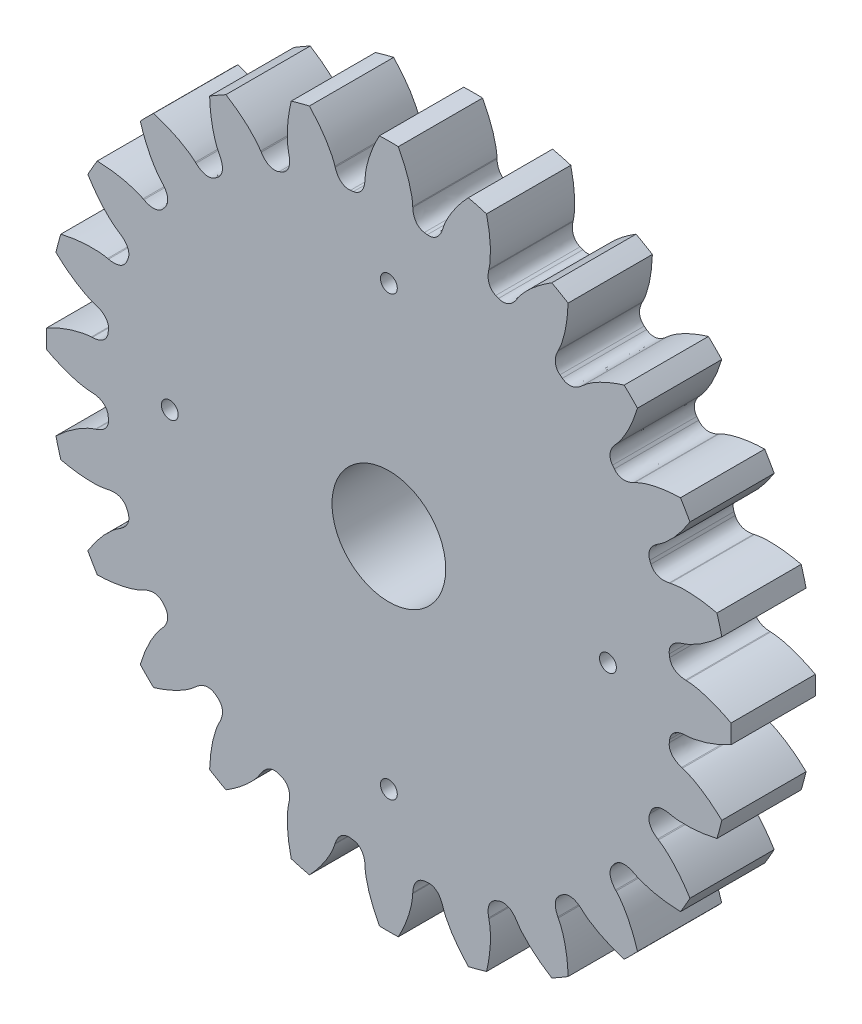
SolidWorks part; units mm, degrees
material "PET"
ref_plane "Front Plane" through (0, 0, 0) normal (0, 0, 1) x (1, 0, 0)
ref_plane "Top Plane" through (0, 0, 0) normal (0, 1, 0) x (1, 0, 0)
ref_plane "Right Plane" through (0, 0, 0) normal (1, 0, 0) x (0, 0, -1)
sketch "Sketch1" plane through (0, 0, 0) normal (0, 0, 1) x (1, 0, 0)
  line L2 (3.0163, 8.479) -> (3.0105, 8.452)
  line L3 (3.8478, 8.1052) -> (3.8627, 8.1284)
  line L4 (5.8144, 6.8332) -> (5.8349, 6.8516)
  line L5 (5.108, 7.4094) -> (5.0955, 7.3849)
  line L6 (7.3849, 5.0955) -> (7.4094, 5.108)
  line L7 (6.8516, 5.8349) -> (6.8332, 5.8144)
  line L8 (8.452, 3.0105) -> (8.479, 3.0163)
  line L9 (8.1284, 3.8627) -> (8.1052, 3.8478)
  line L10 (8.9432, 0.7204) -> (8.9707, 0.719)
  line L11 (8.8511, 1.6273) -> (8.8249, 1.6189)
  line L12 (8.8249, -1.6189) -> (8.8511, -1.6273)
  line L13 (8.9707, -0.719) -> (8.9432, -0.7204)
  line L14 (8.1052, -3.8478) -> (8.1284, -3.8627)
  line L15 (8.479, -3.0163) -> (8.452, -3.0105)
  line L16 (6.8332, -5.8144) -> (6.8516, -5.8349)
  line L17 (7.4094, -5.108) -> (7.3849, -5.0955)
  line L18 (5.0955, -7.3849) -> (5.108, -7.4094)
  line L19 (5.8349, -6.8516) -> (5.8144, -6.8332)
  line L20 (3.0105, -8.452) -> (3.0163, -8.479)
  line L21 (3.8627, -8.1284) -> (3.8478, -8.1052)
  line L22 (0.7204, -8.9432) -> (0.719, -8.9707)
  line L23 (1.6273, -8.8511) -> (1.6189, -8.8249)
  line L24 (-1.6189, -8.8249) -> (-1.6273, -8.8511)
  line L25 (-0.719, -8.9707) -> (-0.7204, -8.9432)
  line L26 (-3.8478, -8.1052) -> (-3.8627, -8.1284)
  line L27 (-3.0163, -8.479) -> (-3.0105, -8.452)
  line L28 (-5.8144, -6.8332) -> (-5.8349, -6.8516)
  line L29 (-5.108, -7.4094) -> (-5.0955, -7.3849)
  line L30 (-7.3849, -5.0955) -> (-7.4094, -5.108)
  line L31 (-6.8516, -5.8349) -> (-6.8332, -5.8144)
  line L32 (-8.452, -3.0105) -> (-8.479, -3.0163)
  line L33 (-8.1284, -3.8627) -> (-8.1052, -3.8478)
  line L34 (-8.9432, -0.7204) -> (-8.9707, -0.719)
  line L35 (-8.8511, -1.6273) -> (-8.8249, -1.6189)
  line L36 (-8.8249, 1.6189) -> (-8.8511, 1.6273)
  line L37 (-8.9707, 0.719) -> (-8.9432, 0.7204)
  line L38 (-8.1052, 3.8478) -> (-8.1284, 3.8627)
  line L39 (-8.479, 3.0163) -> (-8.452, 3.0105)
  line L40 (-6.8332, 5.8144) -> (-6.8516, 5.8349)
  line L41 (-7.4094, 5.108) -> (-7.3849, 5.0955)
  line L42 (-5.0955, 7.3849) -> (-5.108, 7.4094)
  line L43 (-5.8349, 6.8516) -> (-5.8144, 6.8332)
  line L44 (-3.0105, 8.452) -> (-3.0163, 8.479)
  line L45 (-3.8627, 8.1284) -> (-3.8478, 8.1052)
  line L46 (-0.7204, 8.9432) -> (-0.719, 8.9707)
  line L47 (-1.6273, 8.8511) -> (-1.6189, 8.8249)
  line L48 (1.6189, 8.8249) -> (1.6273, 8.8511)
  line L49 (0.719, 8.9707) -> (0.7204, 8.9432)
  arc A1 (5.4033, 8.7909) -> (4.9115, 9.0749) centre (0, 0) ccw
  arc A3 (3.3076, 7.8657) -> (3.223, 7.9007) centre (0, 0) ccw
  arc A4 (7.4945, 7.0929) -> (7.0929, 7.4945) centre (0, 0) ccw
  arc A5 (5.2307, 6.7416) -> (5.1581, 6.7973) centre (0, 0) ccw
  arc A6 (9.0749, 4.9115) -> (8.7909, 5.4033) centre (0, 0) ccw
  arc A7 (6.7973, 5.1581) -> (6.7416, 5.2307) centre (0, 0) ccw
  arc A8 (10.0369, 2.3954) -> (9.8899, 2.944) centre (0, 0) ccw
  arc A9 (7.9007, 3.223) -> (7.8657, 3.3076) centre (0, 0) ccw
  arc A10 (10.3148, -0.284) -> (10.3148, 0.284) centre (0, 0) ccw
  arc A11 (8.4657, 1.0684) -> (8.4537, 1.1591) centre (0, 0) ccw
  arc A12 (9.8899, -2.944) -> (10.0369, -2.3954) centre (0, 0) ccw
  arc A13 (8.4537, -1.1591) -> (8.4657, -1.0684) centre (0, 0) ccw
  arc A14 (8.7909, -5.4033) -> (9.0749, -4.9115) centre (0, 0) ccw
  arc A15 (7.8657, -3.3076) -> (7.9007, -3.223) centre (0, 0) ccw
  arc A16 (7.0929, -7.4945) -> (7.4945, -7.0929) centre (0, 0) ccw
  arc A17 (6.7416, -5.2307) -> (6.7973, -5.1581) centre (0, 0) ccw
  arc A18 (4.9115, -9.0749) -> (5.4033, -8.7909) centre (0, 0) ccw
  arc A19 (5.1581, -6.7973) -> (5.2307, -6.7416) centre (0, 0) ccw
  arc A20 (2.3954, -10.0369) -> (2.944, -9.8899) centre (0, 0) ccw
  arc A21 (3.223, -7.9007) -> (3.3076, -7.8657) centre (0, 0) ccw
  arc A22 (-0.284, -10.3148) -> (0.284, -10.3148) centre (0, 0) ccw
  arc A23 (1.0684, -8.4657) -> (1.1591, -8.4537) centre (0, 0) ccw
  arc A24 (-2.944, -9.8899) -> (-2.3954, -10.0369) centre (0, 0) ccw
  arc A25 (-1.1591, -8.4537) -> (-1.0684, -8.4657) centre (0, 0) ccw
  arc A26 (-5.4033, -8.7909) -> (-4.9115, -9.0749) centre (0, 0) ccw
  arc A27 (-3.3076, -7.8657) -> (-3.223, -7.9007) centre (0, 0) ccw
  arc A28 (-7.4945, -7.0929) -> (-7.0929, -7.4945) centre (0, 0) ccw
  arc A29 (-5.2307, -6.7416) -> (-5.1581, -6.7973) centre (0, 0) ccw
  arc A30 (-9.0749, -4.9115) -> (-8.7909, -5.4033) centre (0, 0) ccw
  arc A31 (-6.7973, -5.1581) -> (-6.7416, -5.2307) centre (0, 0) ccw
  arc A32 (-10.0369, -2.3954) -> (-9.8899, -2.944) centre (0, 0) ccw
  arc A33 (-7.9007, -3.223) -> (-7.8657, -3.3076) centre (0, 0) ccw
  arc A34 (-10.3148, 0.284) -> (-10.3148, -0.284) centre (0, 0) ccw
  arc A35 (-8.4657, -1.0684) -> (-8.4537, -1.1591) centre (0, 0) ccw
  arc A36 (-9.8899, 2.944) -> (-10.0369, 2.3954) centre (0, 0) ccw
  arc A37 (-8.4537, 1.1591) -> (-8.4657, 1.0684) centre (0, 0) ccw
  arc A38 (-8.7909, 5.4033) -> (-9.0749, 4.9115) centre (0, 0) ccw
  arc A39 (-7.8657, 3.3076) -> (-7.9007, 3.223) centre (0, 0) ccw
  arc A40 (-7.0929, 7.4945) -> (-7.4945, 7.0929) centre (0, 0) ccw
  arc A41 (-6.7416, 5.2307) -> (-6.7973, 5.1581) centre (0, 0) ccw
  arc A42 (-4.9115, 9.0749) -> (-5.4033, 8.7909) centre (0, 0) ccw
  arc A43 (-5.1581, 6.7973) -> (-5.2307, 6.7416) centre (0, 0) ccw
  arc A44 (-2.3954, 10.0369) -> (-2.944, 9.8899) centre (0, 0) ccw
  arc A45 (-3.223, 7.9007) -> (-3.3076, 7.8657) centre (0, 0) ccw
  arc A46 (0.284, 10.3148) -> (-0.284, 10.3148) centre (0, 0) ccw
  arc A47 (-1.0684, 8.4657) -> (-1.1591, 8.4537) centre (0, 0) ccw
  arc A48 (2.944, 9.8899) -> (2.3954, 10.0369) centre (0, 0) ccw
  arc A49 (1.1591, 8.4537) -> (1.0684, 8.4657) centre (0, 0) ccw
  spline S1 degree 3 poles (3.8627, 8.1284) (3.8914, 8.1749) (3.9475, 8.2534) (4.0419, 8.3672) (4.1469, 8.48) (4.2788, 8.6067) (4.4396, 8.7446) (4.6307, 8.8906) (4.7925, 9.0003) (4.8899, 9.0615) (4.9115, 9.0749) knots 0.278297 0.278297 0.278297 0.278297 0.361423 0.4249 0.502987 0.595682 0.702987 0.8249 0.961423 1 1 1 1
  spline S3 degree 3 poles (3.3076, 7.8657) (3.3668, 7.8404) (3.4599, 7.8298) (3.5701, 7.8582) (3.6332, 7.8877) (3.6849, 7.9217) (3.7286, 7.9585) (3.7669, 7.9973) (3.8073, 8.0456) (3.8335, 8.0821) (3.8478, 8.1052) knots 0 0 0 0 0.297543 0.420013 0.525832 0.620051 0.707292 0.791048 0.873798 1 1 1 1
  spline S6 degree 3 poles (2.944, 9.8899) (2.9498, 9.8652) (2.9754, 9.7529) (3.0122, 9.561) (3.0441, 9.3226) (3.0603, 9.1114) (3.064, 8.9285) (3.0584, 8.7745) (3.0447, 8.6274) (3.0289, 8.5322) (3.0163, 8.479) knots 0 0 0 0 0.038577 0.1751 0.297013 0.404318 0.497013 0.5751 0.638577 0.721703 0.721703 0.721703 0.721703
  spline S7 degree 3 poles (3.0105, 8.452) (3.0042, 8.4256) (2.9969, 8.3813) (2.9914, 8.3186) (2.991, 8.264) (2.9959, 8.2071) (3.0084, 8.1465) (3.0321, 8.081) (3.09, 7.9831) (3.1633, 7.9247) (3.223, 7.9007) knots 0 0 0 0 0.126202 0.208952 0.292708 0.379949 0.474168 0.579987 0.702457 1 1 1 1
  spline S8 degree 3 poles (5.8349, 6.8516) (5.8746, 6.8892) (5.9492, 6.9505) (6.0698, 7.0359) (6.2004, 7.1178) (6.3606, 7.206) (6.5515, 7.2976) (6.774, 7.3892) (6.9586, 7.4532) (7.0686, 7.4872) (7.0929, 7.4945) knots 0.278297 0.278297 0.278297 0.278297 0.361423 0.4249 0.502987 0.595682 0.702987 0.8249 0.961423 1 1 1 1
  spline S9 degree 3 poles (5.2307, 6.7416) (5.2813, 6.7019) (5.3685, 6.6675) (5.4823, 6.6664) (5.5509, 6.6785) (5.6096, 6.6981) (5.6613, 6.7223) (5.7084, 6.7499) (5.76, 6.786) (5.7947, 6.8146) (5.8144, 6.8332) knots 0 0 0 0 0.297543 0.420013 0.525832 0.620051 0.707292 0.791048 0.873798 1 1 1 1
  spline S10 degree 3 poles (5.0955, 7.3849) (5.0826, 7.361) (5.064, 7.32) (5.0425, 7.2609) (5.0279, 7.2083) (5.018, 7.1521) (5.0143, 7.0903) (5.0203, 7.0209) (5.0509, 6.9113) (5.1066, 6.8359) (5.1581, 6.7973) knots 0 0 0 0 0.126202 0.208952 0.292708 0.379949 0.474168 0.579987 0.702457 1 1 1 1
  spline S11 degree 3 poles (5.4033, 8.7909) (5.4026, 8.7656) (5.3982, 8.6505) (5.3841, 8.4557) (5.3532, 8.217) (5.3142, 8.0089) (5.2704, 7.8313) (5.2252, 7.684) (5.1739, 7.5454) (5.134, 7.4575) (5.108, 7.4094) knots 0 0 0 0 0.038577 0.1751 0.297013 0.404318 0.497013 0.5751 0.638577 0.721703 0.721703 0.721703 0.721703
  spline S12 degree 3 poles (7.4094, 5.108) (7.4575, 5.134) (7.5454, 5.1739) (7.684, 5.2252) (7.8313, 5.2704) (8.0089, 5.3142) (8.217, 5.3532) (8.4557, 5.3841) (8.6505, 5.3982) (8.7656, 5.4026) (8.7909, 5.4033) knots 0.278297 0.278297 0.278297 0.278297 0.361423 0.4249 0.502987 0.595682 0.702987 0.8249 0.961423 1 1 1 1
  spline S13 degree 3 poles (6.7973, 5.1581) (6.8359, 5.1066) (6.9113, 5.0509) (7.0209, 5.0203) (7.0903, 5.0143) (7.1521, 5.018) (7.2083, 5.0279) (7.2609, 5.0425) (7.32, 5.064) (7.361, 5.0826) (7.3849, 5.0955) knots 0 0 0 0 0.297543 0.420013 0.525832 0.620051 0.707292 0.791048 0.873798 1 1 1 1
  spline S14 degree 3 poles (6.8332, 5.8144) (6.8146, 5.7947) (6.786, 5.76) (6.7499, 5.7084) (6.7223, 5.6613) (6.6981, 5.6096) (6.6785, 5.5509) (6.6664, 5.4823) (6.6675, 5.3685) (6.7019, 5.2813) (6.7416, 5.2307) knots 0 0 0 0 0.126202 0.208952 0.292708 0.379949 0.474168 0.579987 0.702457 1 1 1 1
  spline S15 degree 3 poles (7.4945, 7.0929) (7.4872, 7.0686) (7.4532, 6.9586) (7.3892, 6.774) (7.2976, 6.5515) (7.206, 6.3606) (7.1178, 6.2004) (7.0359, 6.0698) (6.9505, 5.9492) (6.8892, 5.8746) (6.8516, 5.8349) knots 0 0 0 0 0.038577 0.1751 0.297013 0.404318 0.497013 0.5751 0.638577 0.721703 0.721703 0.721703 0.721703
  spline S16 degree 3 poles (8.479, 3.0163) (8.5322, 3.0289) (8.6274, 3.0447) (8.7745, 3.0584) (8.9285, 3.064) (9.1114, 3.0603) (9.3226, 3.0441) (9.561, 3.0122) (9.7529, 2.9754) (9.8652, 2.9498) (9.8899, 2.944) knots 0.278297 0.278297 0.278297 0.278297 0.361423 0.4249 0.502987 0.595682 0.702987 0.8249 0.961423 1 1 1 1
  spline S17 degree 3 poles (7.9007, 3.223) (7.9247, 3.1633) (7.9831, 3.09) (8.081, 3.0321) (8.1465, 3.0084) (8.2071, 2.9959) (8.264, 2.991) (8.3186, 2.9914) (8.3813, 2.9969) (8.4256, 3.0042) (8.452, 3.0105) knots 0 0 0 0 0.297543 0.420013 0.525832 0.620051 0.707292 0.791048 0.873798 1 1 1 1
  spline S18 degree 3 poles (8.1052, 3.8478) (8.0821, 3.8335) (8.0456, 3.8073) (7.9973, 3.7669) (7.9585, 3.7286) (7.9217, 3.6849) (7.8877, 3.6332) (7.8582, 3.5701) (7.8298, 3.4599) (7.8404, 3.3668) (7.8657, 3.3076) knots 0 0 0 0 0.126202 0.208952 0.292708 0.379949 0.474168 0.579987 0.702457 1 1 1 1
  spline S19 degree 3 poles (9.0749, 4.9115) (9.0615, 4.8899) (9.0003, 4.7925) (8.8906, 4.6307) (8.7446, 4.4396) (8.6067, 4.2788) (8.48, 4.1469) (8.3672, 4.0419) (8.2534, 3.9475) (8.1749, 3.8914) (8.1284, 3.8627) knots 0 0 0 0 0.038577 0.1751 0.297013 0.404318 0.497013 0.5751 0.638577 0.721703 0.721703 0.721703 0.721703
  spline S20 degree 3 poles (8.9707, 0.719) (9.0254, 0.7175) (9.1214, 0.7081) (9.2671, 0.6832) (9.4173, 0.6487) (9.593, 0.5978) (9.7928, 0.5275) (10.0149, 0.435) (10.1907, 0.3497) (10.2925, 0.296) (10.3148, 0.284) knots 0.278297 0.278297 0.278297 0.278297 0.361423 0.4249 0.502987 0.595682 0.702987 0.8249 0.961423 1 1 1 1
  spline S21 degree 3 poles (8.4657, 1.0684) (8.4734, 1.0045) (8.5108, 0.9185) (8.5905, 0.8373) (8.6475, 0.7974) (8.7029, 0.7697) (8.7565, 0.7502) (8.8094, 0.7364) (8.8713, 0.7255) (8.9161, 0.7212) (8.9432, 0.7204) knots 0 0 0 0 0.297543 0.420013 0.525832 0.620051 0.707292 0.791048 0.873798 1 1 1 1
  spline S22 degree 3 poles (8.8249, 1.6189) (8.7989, 1.6111) (8.7568, 1.5953) (8.6998, 1.5687) (8.6523, 1.5417) (8.6055, 1.509) (8.5592, 1.4679) (8.5145, 1.4146) (8.4585, 1.3155) (8.4447, 1.2228) (8.4537, 1.1591) knots 0 0 0 0 0.126202 0.208952 0.292708 0.379949 0.474168 0.579987 0.702457 1 1 1 1
  spline S23 degree 3 poles (10.0369, 2.3954) (10.0184, 2.378) (9.934, 2.2997) (9.7862, 2.1719) (9.5956, 2.025) (9.4209, 1.9054) (9.2643, 1.8108) (9.1282, 1.7386) (8.9939, 1.6769) (8.9035, 1.6429) (8.8511, 1.6273) knots 0 0 0 0 0.038577 0.1751 0.297013 0.404318 0.497013 0.5751 0.638577 0.721703 0.721703 0.721703 0.721703
  spline S24 degree 3 poles (8.8511, -1.6273) (8.9035, -1.6429) (8.9939, -1.6769) (9.1282, -1.7386) (9.2643, -1.8108) (9.4209, -1.9054) (9.5956, -2.025) (9.7862, -2.1719) (9.934, -2.2997) (10.0184, -2.378) (10.0369, -2.3954) knots 0.278297 0.278297 0.278297 0.278297 0.361423 0.4249 0.502987 0.595682 0.702987 0.8249 0.961423 1 1 1 1
  spline S25 degree 3 poles (8.4537, -1.1591) (8.4447, -1.2228) (8.4585, -1.3155) (8.5145, -1.4146) (8.5592, -1.4679) (8.6055, -1.509) (8.6523, -1.5417) (8.6998, -1.5687) (8.7568, -1.5953) (8.7989, -1.6111) (8.8249, -1.6189) knots 0 0 0 0 0.297543 0.420013 0.525832 0.620051 0.707292 0.791048 0.873798 1 1 1 1
  spline S26 degree 3 poles (8.9432, -0.7204) (8.9161, -0.7212) (8.8713, -0.7255) (8.8094, -0.7364) (8.7565, -0.7502) (8.7029, -0.7697) (8.6475, -0.7974) (8.5905, -0.8373) (8.5108, -0.9185) (8.4734, -1.0045) (8.4657, -1.0684) knots 0 0 0 0 0.126202 0.208952 0.292708 0.379949 0.474168 0.579987 0.702457 1 1 1 1
  spline S27 degree 3 poles (10.3148, -0.284) (10.2925, -0.296) (10.1907, -0.3497) (10.0149, -0.435) (9.7928, -0.5275) (9.593, -0.5978) (9.4173, -0.6487) (9.2671, -0.6832) (9.1214, -0.7081) (9.0254, -0.7175) (8.9707, -0.719) knots 0 0 0 0 0.038577 0.1751 0.297013 0.404318 0.497013 0.5751 0.638577 0.721703 0.721703 0.721703 0.721703
  spline S28 degree 3 poles (8.1284, -3.8627) (8.1749, -3.8914) (8.2534, -3.9475) (8.3672, -4.0419) (8.48, -4.1469) (8.6067, -4.2788) (8.7446, -4.4396) (8.8906, -4.6307) (9.0003, -4.7925) (9.0615, -4.8899) (9.0749, -4.9115) knots 0.278297 0.278297 0.278297 0.278297 0.361423 0.4249 0.502987 0.595682 0.702987 0.8249 0.961423 1 1 1 1
  spline S29 degree 3 poles (7.8657, -3.3076) (7.8404, -3.3668) (7.8298, -3.4599) (7.8582, -3.5701) (7.8877, -3.6332) (7.9217, -3.6849) (7.9585, -3.7286) (7.9973, -3.7669) (8.0456, -3.8073) (8.0821, -3.8335) (8.1052, -3.8478) knots 0 0 0 0 0.297543 0.420013 0.525832 0.620051 0.707292 0.791048 0.873798 1 1 1 1
  spline S30 degree 3 poles (8.452, -3.0105) (8.4256, -3.0042) (8.3813, -2.9969) (8.3186, -2.9914) (8.264, -2.991) (8.2071, -2.9959) (8.1465, -3.0084) (8.081, -3.0321) (7.9831, -3.09) (7.9247, -3.1633) (7.9007, -3.223) knots 0 0 0 0 0.126202 0.208952 0.292708 0.379949 0.474168 0.579987 0.702457 1 1 1 1
  spline S31 degree 3 poles (9.8899, -2.944) (9.8652, -2.9498) (9.7529, -2.9754) (9.561, -3.0122) (9.3226, -3.0441) (9.1114, -3.0603) (8.9285, -3.064) (8.7745, -3.0584) (8.6274, -3.0447) (8.5322, -3.0289) (8.479, -3.0163) knots 0 0 0 0 0.038577 0.1751 0.297013 0.404318 0.497013 0.5751 0.638577 0.721703 0.721703 0.721703 0.721703
  spline S32 degree 3 poles (6.8516, -5.8349) (6.8892, -5.8746) (6.9505, -5.9492) (7.0359, -6.0698) (7.1178, -6.2004) (7.206, -6.3606) (7.2976, -6.5515) (7.3892, -6.774) (7.4532, -6.9586) (7.4872, -7.0686) (7.4945, -7.0929) knots 0.278297 0.278297 0.278297 0.278297 0.361423 0.4249 0.502987 0.595682 0.702987 0.8249 0.961423 1 1 1 1
  spline S33 degree 3 poles (6.7416, -5.2307) (6.7019, -5.2813) (6.6675, -5.3685) (6.6664, -5.4823) (6.6785, -5.5509) (6.6981, -5.6096) (6.7223, -5.6613) (6.7499, -5.7084) (6.786, -5.76) (6.8146, -5.7947) (6.8332, -5.8144) knots 0 0 0 0 0.297543 0.420013 0.525832 0.620051 0.707292 0.791048 0.873798 1 1 1 1
  spline S34 degree 3 poles (7.3849, -5.0955) (7.361, -5.0826) (7.32, -5.064) (7.2609, -5.0425) (7.2083, -5.0279) (7.1521, -5.018) (7.0903, -5.0143) (7.0209, -5.0203) (6.9113, -5.0509) (6.8359, -5.1066) (6.7973, -5.1581) knots 0 0 0 0 0.126202 0.208952 0.292708 0.379949 0.474168 0.579987 0.702457 1 1 1 1
  spline S35 degree 3 poles (8.7909, -5.4033) (8.7656, -5.4026) (8.6505, -5.3982) (8.4557, -5.3841) (8.217, -5.3532) (8.0089, -5.3142) (7.8313, -5.2704) (7.684, -5.2252) (7.5454, -5.1739) (7.4575, -5.134) (7.4094, -5.108) knots 0 0 0 0 0.038577 0.1751 0.297013 0.404318 0.497013 0.5751 0.638577 0.721703 0.721703 0.721703 0.721703
  spline S36 degree 3 poles (5.108, -7.4094) (5.134, -7.4575) (5.1739, -7.5454) (5.2252, -7.684) (5.2704, -7.8313) (5.3142, -8.0089) (5.3532, -8.217) (5.3841, -8.4557) (5.3982, -8.6505) (5.4026, -8.7656) (5.4033, -8.7909) knots 0.278297 0.278297 0.278297 0.278297 0.361423 0.4249 0.502987 0.595682 0.702987 0.8249 0.961423 1 1 1 1
  spline S37 degree 3 poles (5.1581, -6.7973) (5.1066, -6.8359) (5.0509, -6.9113) (5.0203, -7.0209) (5.0143, -7.0903) (5.018, -7.1521) (5.0279, -7.2083) (5.0425, -7.2609) (5.064, -7.32) (5.0826, -7.361) (5.0955, -7.3849) knots 0 0 0 0 0.297543 0.420013 0.525832 0.620051 0.707292 0.791048 0.873798 1 1 1 1
  spline S38 degree 3 poles (5.8144, -6.8332) (5.7947, -6.8146) (5.76, -6.786) (5.7084, -6.7499) (5.6613, -6.7223) (5.6096, -6.6981) (5.5509, -6.6785) (5.4823, -6.6664) (5.3685, -6.6675) (5.2813, -6.7019) (5.2307, -6.7416) knots 0 0 0 0 0.126202 0.208952 0.292708 0.379949 0.474168 0.579987 0.702457 1 1 1 1
  spline S39 degree 3 poles (7.0929, -7.4945) (7.0686, -7.4872) (6.9586, -7.4532) (6.774, -7.3892) (6.5515, -7.2976) (6.3606, -7.206) (6.2004, -7.1178) (6.0698, -7.0359) (5.9492, -6.9505) (5.8746, -6.8892) (5.8349, -6.8516) knots 0 0 0 0 0.038577 0.1751 0.297013 0.404318 0.497013 0.5751 0.638577 0.721703 0.721703 0.721703 0.721703
  spline S40 degree 3 poles (3.0163, -8.479) (3.0289, -8.5322) (3.0447, -8.6274) (3.0584, -8.7745) (3.064, -8.9285) (3.0603, -9.1114) (3.0441, -9.3226) (3.0122, -9.561) (2.9754, -9.7529) (2.9498, -9.8652) (2.944, -9.8899) knots 0.278297 0.278297 0.278297 0.278297 0.361423 0.4249 0.502987 0.595682 0.702987 0.8249 0.961423 1 1 1 1
  spline S41 degree 3 poles (3.223, -7.9007) (3.1633, -7.9247) (3.09, -7.9831) (3.0321, -8.081) (3.0084, -8.1465) (2.9959, -8.2071) (2.991, -8.264) (2.9914, -8.3186) (2.9969, -8.3813) (3.0042, -8.4256) (3.0105, -8.452) knots 0 0 0 0 0.297543 0.420013 0.525832 0.620051 0.707292 0.791048 0.873798 1 1 1 1
  spline S42 degree 3 poles (3.8478, -8.1052) (3.8335, -8.0821) (3.8073, -8.0456) (3.7669, -7.9973) (3.7286, -7.9585) (3.6849, -7.9217) (3.6332, -7.8877) (3.5701, -7.8582) (3.4599, -7.8298) (3.3668, -7.8404) (3.3076, -7.8657) knots 0 0 0 0 0.126202 0.208952 0.292708 0.379949 0.474168 0.579987 0.702457 1 1 1 1
  spline S43 degree 3 poles (4.9115, -9.0749) (4.8899, -9.0615) (4.7925, -9.0003) (4.6307, -8.8906) (4.4396, -8.7446) (4.2788, -8.6067) (4.1469, -8.48) (4.0419, -8.3672) (3.9475, -8.2534) (3.8914, -8.1749) (3.8627, -8.1284) knots 0 0 0 0 0.038577 0.1751 0.297013 0.404318 0.497013 0.5751 0.638577 0.721703 0.721703 0.721703 0.721703
  spline S44 degree 3 poles (0.719, -8.9707) (0.7175, -9.0254) (0.7081, -9.1214) (0.6832, -9.2671) (0.6487, -9.4173) (0.5978, -9.593) (0.5275, -9.7928) (0.435, -10.0149) (0.3497, -10.1907) (0.296, -10.2925) (0.284, -10.3148) knots 0.278297 0.278297 0.278297 0.278297 0.361423 0.4249 0.502987 0.595682 0.702987 0.8249 0.961423 1 1 1 1
  spline S45 degree 3 poles (1.0684, -8.4657) (1.0045, -8.4734) (0.9185, -8.5108) (0.8373, -8.5905) (0.7974, -8.6475) (0.7697, -8.7029) (0.7502, -8.7565) (0.7364, -8.8094) (0.7255, -8.8713) (0.7212, -8.9161) (0.7204, -8.9432) knots 0 0 0 0 0.297543 0.420013 0.525832 0.620051 0.707292 0.791048 0.873798 1 1 1 1
  spline S46 degree 3 poles (1.6189, -8.8249) (1.6111, -8.7989) (1.5953, -8.7568) (1.5687, -8.6998) (1.5417, -8.6523) (1.509, -8.6055) (1.4679, -8.5592) (1.4146, -8.5145) (1.3155, -8.4585) (1.2228, -8.4447) (1.1591, -8.4537) knots 0 0 0 0 0.126202 0.208952 0.292708 0.379949 0.474168 0.579987 0.702457 1 1 1 1
  spline S47 degree 3 poles (2.3954, -10.0369) (2.378, -10.0184) (2.2997, -9.934) (2.1719, -9.7862) (2.025, -9.5956) (1.9054, -9.4209) (1.8108, -9.2643) (1.7386, -9.1282) (1.6769, -8.9939) (1.6429, -8.9035) (1.6273, -8.8511) knots 0 0 0 0 0.038577 0.1751 0.297013 0.404318 0.497013 0.5751 0.638577 0.721703 0.721703 0.721703 0.721703
  spline S48 degree 3 poles (-1.6273, -8.8511) (-1.6429, -8.9035) (-1.6769, -8.9939) (-1.7386, -9.1282) (-1.8108, -9.2643) (-1.9054, -9.4209) (-2.025, -9.5956) (-2.1719, -9.7862) (-2.2997, -9.934) (-2.378, -10.0184) (-2.3954, -10.0369) knots 0.278297 0.278297 0.278297 0.278297 0.361423 0.4249 0.502987 0.595682 0.702987 0.8249 0.961423 1 1 1 1
  spline S49 degree 3 poles (-1.1591, -8.4537) (-1.2228, -8.4447) (-1.3155, -8.4585) (-1.4146, -8.5145) (-1.4679, -8.5592) (-1.509, -8.6055) (-1.5417, -8.6523) (-1.5687, -8.6998) (-1.5953, -8.7568) (-1.6111, -8.7989) (-1.6189, -8.8249) knots 0 0 0 0 0.297543 0.420013 0.525832 0.620051 0.707292 0.791048 0.873798 1 1 1 1
  spline S50 degree 3 poles (-0.7204, -8.9432) (-0.7212, -8.9161) (-0.7255, -8.8713) (-0.7364, -8.8094) (-0.7502, -8.7565) (-0.7697, -8.7029) (-0.7974, -8.6475) (-0.8373, -8.5905) (-0.9185, -8.5108) (-1.0045, -8.4734) (-1.0684, -8.4657) knots 0 0 0 0 0.126202 0.208952 0.292708 0.379949 0.474168 0.579987 0.702457 1 1 1 1
  spline S51 degree 3 poles (-0.284, -10.3148) (-0.296, -10.2925) (-0.3497, -10.1907) (-0.435, -10.0149) (-0.5275, -9.7928) (-0.5978, -9.593) (-0.6487, -9.4173) (-0.6832, -9.2671) (-0.7081, -9.1214) (-0.7175, -9.0254) (-0.719, -8.9707) knots 0 0 0 0 0.038577 0.1751 0.297013 0.404318 0.497013 0.5751 0.638577 0.721703 0.721703 0.721703 0.721703
  spline S52 degree 3 poles (-3.8627, -8.1284) (-3.8914, -8.1749) (-3.9475, -8.2534) (-4.0419, -8.3672) (-4.1469, -8.48) (-4.2788, -8.6067) (-4.4396, -8.7446) (-4.6307, -8.8906) (-4.7925, -9.0003) (-4.8899, -9.0615) (-4.9115, -9.0749) knots 0.278297 0.278297 0.278297 0.278297 0.361423 0.4249 0.502987 0.595682 0.702987 0.8249 0.961423 1 1 1 1
  spline S53 degree 3 poles (-3.3076, -7.8657) (-3.3668, -7.8404) (-3.4599, -7.8298) (-3.5701, -7.8582) (-3.6332, -7.8877) (-3.6849, -7.9217) (-3.7286, -7.9585) (-3.7669, -7.9973) (-3.8073, -8.0456) (-3.8335, -8.0821) (-3.8478, -8.1052) knots 0 0 0 0 0.297543 0.420013 0.525832 0.620051 0.707292 0.791048 0.873798 1 1 1 1
  spline S54 degree 3 poles (-3.0105, -8.452) (-3.0042, -8.4256) (-2.9969, -8.3813) (-2.9914, -8.3186) (-2.991, -8.264) (-2.9959, -8.2071) (-3.0084, -8.1465) (-3.0321, -8.081) (-3.09, -7.9831) (-3.1633, -7.9247) (-3.223, -7.9007) knots 0 0 0 0 0.126202 0.208952 0.292708 0.379949 0.474168 0.579987 0.702457 1 1 1 1
  spline S55 degree 3 poles (-2.944, -9.8899) (-2.9498, -9.8652) (-2.9754, -9.7529) (-3.0122, -9.561) (-3.0441, -9.3226) (-3.0603, -9.1114) (-3.064, -8.9285) (-3.0584, -8.7745) (-3.0447, -8.6274) (-3.0289, -8.5322) (-3.0163, -8.479) knots 0 0 0 0 0.038577 0.1751 0.297013 0.404318 0.497013 0.5751 0.638577 0.721703 0.721703 0.721703 0.721703
  spline S56 degree 3 poles (-5.8349, -6.8516) (-5.8746, -6.8892) (-5.9492, -6.9505) (-6.0698, -7.0359) (-6.2004, -7.1178) (-6.3606, -7.206) (-6.5515, -7.2976) (-6.774, -7.3892) (-6.9586, -7.4532) (-7.0686, -7.4872) (-7.0929, -7.4945) knots 0.278297 0.278297 0.278297 0.278297 0.361423 0.4249 0.502987 0.595682 0.702987 0.8249 0.961423 1 1 1 1
  spline S57 degree 3 poles (-5.2307, -6.7416) (-5.2813, -6.7019) (-5.3685, -6.6675) (-5.4823, -6.6664) (-5.5509, -6.6785) (-5.6096, -6.6981) (-5.6613, -6.7223) (-5.7084, -6.7499) (-5.76, -6.786) (-5.7947, -6.8146) (-5.8144, -6.8332) knots 0 0 0 0 0.297543 0.420013 0.525832 0.620051 0.707292 0.791048 0.873798 1 1 1 1
  spline S58 degree 3 poles (-5.0955, -7.3849) (-5.0826, -7.361) (-5.064, -7.32) (-5.0425, -7.2609) (-5.0279, -7.2083) (-5.018, -7.1521) (-5.0143, -7.0903) (-5.0203, -7.0209) (-5.0509, -6.9113) (-5.1066, -6.8359) (-5.1581, -6.7973) knots 0 0 0 0 0.126202 0.208952 0.292708 0.379949 0.474168 0.579987 0.702457 1 1 1 1
  spline S59 degree 3 poles (-5.4033, -8.7909) (-5.4026, -8.7656) (-5.3982, -8.6505) (-5.3841, -8.4557) (-5.3532, -8.217) (-5.3142, -8.0089) (-5.2704, -7.8313) (-5.2252, -7.684) (-5.1739, -7.5454) (-5.134, -7.4575) (-5.108, -7.4094) knots 0 0 0 0 0.038577 0.1751 0.297013 0.404318 0.497013 0.5751 0.638577 0.721703 0.721703 0.721703 0.721703
  spline S60 degree 3 poles (-7.4094, -5.108) (-7.4575, -5.134) (-7.5454, -5.1739) (-7.684, -5.2252) (-7.8313, -5.2704) (-8.0089, -5.3142) (-8.217, -5.3532) (-8.4557, -5.3841) (-8.6505, -5.3982) (-8.7656, -5.4026) (-8.7909, -5.4033) knots 0.278297 0.278297 0.278297 0.278297 0.361423 0.4249 0.502987 0.595682 0.702987 0.8249 0.961423 1 1 1 1
  spline S61 degree 3 poles (-6.7973, -5.1581) (-6.8359, -5.1066) (-6.9113, -5.0509) (-7.0209, -5.0203) (-7.0903, -5.0143) (-7.1521, -5.018) (-7.2083, -5.0279) (-7.2609, -5.0425) (-7.32, -5.064) (-7.361, -5.0826) (-7.3849, -5.0955) knots 0 0 0 0 0.297543 0.420013 0.525832 0.620051 0.707292 0.791048 0.873798 1 1 1 1
  spline S62 degree 3 poles (-6.8332, -5.8144) (-6.8146, -5.7947) (-6.786, -5.76) (-6.7499, -5.7084) (-6.7223, -5.6613) (-6.6981, -5.6096) (-6.6785, -5.5509) (-6.6664, -5.4823) (-6.6675, -5.3685) (-6.7019, -5.2813) (-6.7416, -5.2307) knots 0 0 0 0 0.126202 0.208952 0.292708 0.379949 0.474168 0.579987 0.702457 1 1 1 1
  spline S63 degree 3 poles (-7.4945, -7.0929) (-7.4872, -7.0686) (-7.4532, -6.9586) (-7.3892, -6.774) (-7.2976, -6.5515) (-7.206, -6.3606) (-7.1178, -6.2004) (-7.0359, -6.0698) (-6.9505, -5.9492) (-6.8892, -5.8746) (-6.8516, -5.8349) knots 0 0 0 0 0.038577 0.1751 0.297013 0.404318 0.497013 0.5751 0.638577 0.721703 0.721703 0.721703 0.721703
  spline S64 degree 3 poles (-8.479, -3.0163) (-8.5322, -3.0289) (-8.6274, -3.0447) (-8.7745, -3.0584) (-8.9285, -3.064) (-9.1114, -3.0603) (-9.3226, -3.0441) (-9.561, -3.0122) (-9.7529, -2.9754) (-9.8652, -2.9498) (-9.8899, -2.944) knots 0.278297 0.278297 0.278297 0.278297 0.361423 0.4249 0.502987 0.595682 0.702987 0.8249 0.961423 1 1 1 1
  spline S65 degree 3 poles (-7.9007, -3.223) (-7.9247, -3.1633) (-7.9831, -3.09) (-8.081, -3.0321) (-8.1465, -3.0084) (-8.2071, -2.9959) (-8.264, -2.991) (-8.3186, -2.9914) (-8.3813, -2.9969) (-8.4256, -3.0042) (-8.452, -3.0105) knots 0 0 0 0 0.297543 0.420013 0.525832 0.620051 0.707292 0.791048 0.873798 1 1 1 1
  spline S66 degree 3 poles (-8.1052, -3.8478) (-8.0821, -3.8335) (-8.0456, -3.8073) (-7.9973, -3.7669) (-7.9585, -3.7286) (-7.9217, -3.6849) (-7.8877, -3.6332) (-7.8582, -3.5701) (-7.8298, -3.4599) (-7.8404, -3.3668) (-7.8657, -3.3076) knots 0 0 0 0 0.126202 0.208952 0.292708 0.379949 0.474168 0.579987 0.702457 1 1 1 1
  spline S67 degree 3 poles (-9.0749, -4.9115) (-9.0615, -4.8899) (-9.0003, -4.7925) (-8.8906, -4.6307) (-8.7446, -4.4396) (-8.6067, -4.2788) (-8.48, -4.1469) (-8.3672, -4.0419) (-8.2534, -3.9475) (-8.1749, -3.8914) (-8.1284, -3.8627) knots 0 0 0 0 0.038577 0.1751 0.297013 0.404318 0.497013 0.5751 0.638577 0.721703 0.721703 0.721703 0.721703
  spline S68 degree 3 poles (-8.9707, -0.719) (-9.0254, -0.7175) (-9.1214, -0.7081) (-9.2671, -0.6832) (-9.4173, -0.6487) (-9.593, -0.5978) (-9.7928, -0.5275) (-10.0149, -0.435) (-10.1907, -0.3497) (-10.2925, -0.296) (-10.3148, -0.284) knots 0.278297 0.278297 0.278297 0.278297 0.361423 0.4249 0.502987 0.595682 0.702987 0.8249 0.961423 1 1 1 1
  spline S69 degree 3 poles (-8.4657, -1.0684) (-8.4734, -1.0045) (-8.5108, -0.9185) (-8.5905, -0.8373) (-8.6475, -0.7974) (-8.7029, -0.7697) (-8.7565, -0.7502) (-8.8094, -0.7364) (-8.8713, -0.7255) (-8.9161, -0.7212) (-8.9432, -0.7204) knots 0 0 0 0 0.297543 0.420013 0.525832 0.620051 0.707292 0.791048 0.873798 1 1 1 1
  spline S70 degree 3 poles (-8.8249, -1.6189) (-8.7989, -1.6111) (-8.7568, -1.5953) (-8.6998, -1.5687) (-8.6523, -1.5417) (-8.6055, -1.509) (-8.5592, -1.4679) (-8.5145, -1.4146) (-8.4585, -1.3155) (-8.4447, -1.2228) (-8.4537, -1.1591) knots 0 0 0 0 0.126202 0.208952 0.292708 0.379949 0.474168 0.579987 0.702457 1 1 1 1
  spline S71 degree 3 poles (-10.0369, -2.3954) (-10.0184, -2.378) (-9.934, -2.2997) (-9.7862, -2.1719) (-9.5956, -2.025) (-9.4209, -1.9054) (-9.2643, -1.8108) (-9.1282, -1.7386) (-8.9939, -1.6769) (-8.9035, -1.6429) (-8.8511, -1.6273) knots 0 0 0 0 0.038577 0.1751 0.297013 0.404318 0.497013 0.5751 0.638577 0.721703 0.721703 0.721703 0.721703
  spline S72 degree 3 poles (-8.8511, 1.6273) (-8.9035, 1.6429) (-8.9939, 1.6769) (-9.1282, 1.7386) (-9.2643, 1.8108) (-9.4209, 1.9054) (-9.5956, 2.025) (-9.7862, 2.1719) (-9.934, 2.2997) (-10.0184, 2.378) (-10.0369, 2.3954) knots 0.278297 0.278297 0.278297 0.278297 0.361423 0.4249 0.502987 0.595682 0.702987 0.8249 0.961423 1 1 1 1
  spline S73 degree 3 poles (-8.4537, 1.1591) (-8.4447, 1.2228) (-8.4585, 1.3155) (-8.5145, 1.4146) (-8.5592, 1.4679) (-8.6055, 1.509) (-8.6523, 1.5417) (-8.6998, 1.5687) (-8.7568, 1.5953) (-8.7989, 1.6111) (-8.8249, 1.6189) knots 0 0 0 0 0.297543 0.420013 0.525832 0.620051 0.707292 0.791048 0.873798 1 1 1 1
  spline S74 degree 3 poles (-8.9432, 0.7204) (-8.9161, 0.7212) (-8.8713, 0.7255) (-8.8094, 0.7364) (-8.7565, 0.7502) (-8.7029, 0.7697) (-8.6475, 0.7974) (-8.5905, 0.8373) (-8.5108, 0.9185) (-8.4734, 1.0045) (-8.4657, 1.0684) knots 0 0 0 0 0.126202 0.208952 0.292708 0.379949 0.474168 0.579987 0.702457 1 1 1 1
  spline S75 degree 3 poles (-10.3148, 0.284) (-10.2925, 0.296) (-10.1907, 0.3497) (-10.0149, 0.435) (-9.7928, 0.5275) (-9.593, 0.5978) (-9.4173, 0.6487) (-9.2671, 0.6832) (-9.1214, 0.7081) (-9.0254, 0.7175) (-8.9707, 0.719) knots 0 0 0 0 0.038577 0.1751 0.297013 0.404318 0.497013 0.5751 0.638577 0.721703 0.721703 0.721703 0.721703
  spline S76 degree 3 poles (-8.1284, 3.8627) (-8.1749, 3.8914) (-8.2534, 3.9475) (-8.3672, 4.0419) (-8.48, 4.1469) (-8.6067, 4.2788) (-8.7446, 4.4396) (-8.8906, 4.6307) (-9.0003, 4.7925) (-9.0615, 4.8899) (-9.0749, 4.9115) knots 0.278297 0.278297 0.278297 0.278297 0.361423 0.4249 0.502987 0.595682 0.702987 0.8249 0.961423 1 1 1 1
  spline S77 degree 3 poles (-7.8657, 3.3076) (-7.8404, 3.3668) (-7.8298, 3.4599) (-7.8582, 3.5701) (-7.8877, 3.6332) (-7.9217, 3.6849) (-7.9585, 3.7286) (-7.9973, 3.7669) (-8.0456, 3.8073) (-8.0821, 3.8335) (-8.1052, 3.8478) knots 0 0 0 0 0.297543 0.420013 0.525832 0.620051 0.707292 0.791048 0.873798 1 1 1 1
  spline S78 degree 3 poles (-8.452, 3.0105) (-8.4256, 3.0042) (-8.3813, 2.9969) (-8.3186, 2.9914) (-8.264, 2.991) (-8.2071, 2.9959) (-8.1465, 3.0084) (-8.081, 3.0321) (-7.9831, 3.09) (-7.9247, 3.1633) (-7.9007, 3.223) knots 0 0 0 0 0.126202 0.208952 0.292708 0.379949 0.474168 0.579987 0.702457 1 1 1 1
  spline S79 degree 3 poles (-9.8899, 2.944) (-9.8652, 2.9498) (-9.7529, 2.9754) (-9.561, 3.0122) (-9.3226, 3.0441) (-9.1114, 3.0603) (-8.9285, 3.064) (-8.7745, 3.0584) (-8.6274, 3.0447) (-8.5322, 3.0289) (-8.479, 3.0163) knots 0 0 0 0 0.038577 0.1751 0.297013 0.404318 0.497013 0.5751 0.638577 0.721703 0.721703 0.721703 0.721703
  spline S80 degree 3 poles (-6.8516, 5.8349) (-6.8892, 5.8746) (-6.9505, 5.9492) (-7.0359, 6.0698) (-7.1178, 6.2004) (-7.206, 6.3606) (-7.2976, 6.5515) (-7.3892, 6.774) (-7.4532, 6.9586) (-7.4872, 7.0686) (-7.4945, 7.0929) knots 0.278297 0.278297 0.278297 0.278297 0.361423 0.4249 0.502987 0.595682 0.702987 0.8249 0.961423 1 1 1 1
  spline S81 degree 3 poles (-6.7416, 5.2307) (-6.7019, 5.2813) (-6.6675, 5.3685) (-6.6664, 5.4823) (-6.6785, 5.5509) (-6.6981, 5.6096) (-6.7223, 5.6613) (-6.7499, 5.7084) (-6.786, 5.76) (-6.8146, 5.7947) (-6.8332, 5.8144) knots 0 0 0 0 0.297543 0.420013 0.525832 0.620051 0.707292 0.791048 0.873798 1 1 1 1
  spline S82 degree 3 poles (-7.3849, 5.0955) (-7.361, 5.0826) (-7.32, 5.064) (-7.2609, 5.0425) (-7.2083, 5.0279) (-7.1521, 5.018) (-7.0903, 5.0143) (-7.0209, 5.0203) (-6.9113, 5.0509) (-6.8359, 5.1066) (-6.7973, 5.1581) knots 0 0 0 0 0.126202 0.208952 0.292708 0.379949 0.474168 0.579987 0.702457 1 1 1 1
  spline S83 degree 3 poles (-8.7909, 5.4033) (-8.7656, 5.4026) (-8.6505, 5.3982) (-8.4557, 5.3841) (-8.217, 5.3532) (-8.0089, 5.3142) (-7.8313, 5.2704) (-7.684, 5.2252) (-7.5454, 5.1739) (-7.4575, 5.134) (-7.4094, 5.108) knots 0 0 0 0 0.038577 0.1751 0.297013 0.404318 0.497013 0.5751 0.638577 0.721703 0.721703 0.721703 0.721703
  spline S84 degree 3 poles (-5.108, 7.4094) (-5.134, 7.4575) (-5.1739, 7.5454) (-5.2252, 7.684) (-5.2704, 7.8313) (-5.3142, 8.0089) (-5.3532, 8.217) (-5.3841, 8.4557) (-5.3982, 8.6505) (-5.4026, 8.7656) (-5.4033, 8.7909) knots 0.278297 0.278297 0.278297 0.278297 0.361423 0.4249 0.502987 0.595682 0.702987 0.8249 0.961423 1 1 1 1
  spline S85 degree 3 poles (-5.1581, 6.7973) (-5.1066, 6.8359) (-5.0509, 6.9113) (-5.0203, 7.0209) (-5.0143, 7.0903) (-5.018, 7.1521) (-5.0279, 7.2083) (-5.0425, 7.2609) (-5.064, 7.32) (-5.0826, 7.361) (-5.0955, 7.3849) knots 0 0 0 0 0.297543 0.420013 0.525832 0.620051 0.707292 0.791048 0.873798 1 1 1 1
  spline S86 degree 3 poles (-5.8144, 6.8332) (-5.7947, 6.8146) (-5.76, 6.786) (-5.7084, 6.7499) (-5.6613, 6.7223) (-5.6096, 6.6981) (-5.5509, 6.6785) (-5.4823, 6.6664) (-5.3685, 6.6675) (-5.2813, 6.7019) (-5.2307, 6.7416) knots 0 0 0 0 0.126202 0.208952 0.292708 0.379949 0.474168 0.579987 0.702457 1 1 1 1
  spline S87 degree 3 poles (-7.0929, 7.4945) (-7.0686, 7.4872) (-6.9586, 7.4532) (-6.774, 7.3892) (-6.5515, 7.2976) (-6.3606, 7.206) (-6.2004, 7.1178) (-6.0698, 7.0359) (-5.9492, 6.9505) (-5.8746, 6.8892) (-5.8349, 6.8516) knots 0 0 0 0 0.038577 0.1751 0.297013 0.404318 0.497013 0.5751 0.638577 0.721703 0.721703 0.721703 0.721703
  spline S88 degree 3 poles (-3.0163, 8.479) (-3.0289, 8.5322) (-3.0447, 8.6274) (-3.0584, 8.7745) (-3.064, 8.9285) (-3.0603, 9.1114) (-3.0441, 9.3226) (-3.0122, 9.561) (-2.9754, 9.7529) (-2.9498, 9.8652) (-2.944, 9.8899) knots 0.278297 0.278297 0.278297 0.278297 0.361423 0.4249 0.502987 0.595682 0.702987 0.8249 0.961423 1 1 1 1
  spline S89 degree 3 poles (-3.223, 7.9007) (-3.1633, 7.9247) (-3.09, 7.9831) (-3.0321, 8.081) (-3.0084, 8.1465) (-2.9959, 8.2071) (-2.991, 8.264) (-2.9914, 8.3186) (-2.9969, 8.3813) (-3.0042, 8.4256) (-3.0105, 8.452) knots 0 0 0 0 0.297543 0.420013 0.525832 0.620051 0.707292 0.791048 0.873798 1 1 1 1
  spline S90 degree 3 poles (-3.8478, 8.1052) (-3.8335, 8.0821) (-3.8073, 8.0456) (-3.7669, 7.9973) (-3.7286, 7.9585) (-3.6849, 7.9217) (-3.6332, 7.8877) (-3.5701, 7.8582) (-3.4599, 7.8298) (-3.3668, 7.8404) (-3.3076, 7.8657) knots 0 0 0 0 0.126202 0.208952 0.292708 0.379949 0.474168 0.579987 0.702457 1 1 1 1
  spline S91 degree 3 poles (-4.9115, 9.0749) (-4.8899, 9.0615) (-4.7925, 9.0003) (-4.6307, 8.8906) (-4.4396, 8.7446) (-4.2788, 8.6067) (-4.1469, 8.48) (-4.0419, 8.3672) (-3.9475, 8.2534) (-3.8914, 8.1749) (-3.8627, 8.1284) knots 0 0 0 0 0.038577 0.1751 0.297013 0.404318 0.497013 0.5751 0.638577 0.721703 0.721703 0.721703 0.721703
  spline S92 degree 3 poles (-0.719, 8.9707) (-0.7175, 9.0254) (-0.7081, 9.1214) (-0.6832, 9.2671) (-0.6487, 9.4173) (-0.5978, 9.593) (-0.5275, 9.7928) (-0.435, 10.0149) (-0.3497, 10.1907) (-0.296, 10.2925) (-0.284, 10.3148) knots 0.278297 0.278297 0.278297 0.278297 0.361423 0.4249 0.502987 0.595682 0.702987 0.8249 0.961423 1 1 1 1
  spline S93 degree 3 poles (-1.0684, 8.4657) (-1.0045, 8.4734) (-0.9185, 8.5108) (-0.8373, 8.5905) (-0.7974, 8.6475) (-0.7697, 8.7029) (-0.7502, 8.7565) (-0.7364, 8.8094) (-0.7255, 8.8713) (-0.7212, 8.9161) (-0.7204, 8.9432) knots 0 0 0 0 0.297543 0.420013 0.525832 0.620051 0.707292 0.791048 0.873798 1 1 1 1
  spline S94 degree 3 poles (-1.6189, 8.8249) (-1.6111, 8.7989) (-1.5953, 8.7568) (-1.5687, 8.6998) (-1.5417, 8.6523) (-1.509, 8.6055) (-1.4679, 8.5592) (-1.4146, 8.5145) (-1.3155, 8.4585) (-1.2228, 8.4447) (-1.1591, 8.4537) knots 0 0 0 0 0.126202 0.208952 0.292708 0.379949 0.474168 0.579987 0.702457 1 1 1 1
  spline S95 degree 3 poles (-2.3954, 10.0369) (-2.378, 10.0184) (-2.2997, 9.934) (-2.1719, 9.7862) (-2.025, 9.5956) (-1.9054, 9.4209) (-1.8108, 9.2643) (-1.7386, 9.1282) (-1.6769, 8.9939) (-1.6429, 8.9035) (-1.6273, 8.8511) knots 0 0 0 0 0.038577 0.1751 0.297013 0.404318 0.497013 0.5751 0.638577 0.721703 0.721703 0.721703 0.721703
  spline S96 degree 3 poles (1.6273, 8.8511) (1.6429, 8.9035) (1.6769, 8.9939) (1.7386, 9.1282) (1.8108, 9.2643) (1.9054, 9.4209) (2.025, 9.5956) (2.1719, 9.7862) (2.2997, 9.934) (2.378, 10.0184) (2.3954, 10.0369) knots 0.278297 0.278297 0.278297 0.278297 0.361423 0.4249 0.502987 0.595682 0.702987 0.8249 0.961423 1 1 1 1
  spline S97 degree 3 poles (1.1591, 8.4537) (1.2228, 8.4447) (1.3155, 8.4585) (1.4146, 8.5145) (1.4679, 8.5592) (1.509, 8.6055) (1.5417, 8.6523) (1.5687, 8.6998) (1.5953, 8.7568) (1.6111, 8.7989) (1.6189, 8.8249) knots 0 0 0 0 0.297543 0.420013 0.525832 0.620051 0.707292 0.791048 0.873798 1 1 1 1
  spline S98 degree 3 poles (0.7204, 8.9432) (0.7212, 8.9161) (0.7255, 8.8713) (0.7364, 8.8094) (0.7502, 8.7565) (0.7697, 8.7029) (0.7974, 8.6475) (0.8373, 8.5905) (0.9185, 8.5108) (1.0045, 8.4734) (1.0684, 8.4657) knots 0 0 0 0 0.126202 0.208952 0.292708 0.379949 0.474168 0.579987 0.702457 1 1 1 1
  spline S99 degree 3 poles (0.284, 10.3148) (0.296, 10.2925) (0.3497, 10.1907) (0.435, 10.0149) (0.5275, 9.7928) (0.5978, 9.593) (0.6487, 9.4173) (0.6832, 9.2671) (0.7081, 9.1214) (0.7175, 9.0254) (0.719, 8.9707) knots 0 0 0 0 0.038577 0.1751 0.297013 0.404318 0.497013 0.5751 0.638577 0.721703 0.721703 0.721703 0.721703
  point P220 (0, 0)
  dimension "D2" = 10.3187
  dimension "D1" = 24
extrude "Boss-Extrude1" add sketch "Sketch1" along normal blind 2.54 contours S1 A1 S11 L5 S10 A5 S9 L4 S8 A4 S15 L7 S14 A7 S13 L6 S12 A6 S19 L9 S18 A9 S17 L8 S16 A8 S23 L11 S22 A11 S21 L10 S20 A10 S27 L13 S26 A13 S25 L12 S24 A12 S31 L15 S30 A15 S29 L14 S28 A14 S35 L17 S34 A17 S33 L16 S32 A16 S39 L19 S38 A19 S37 L18 S36 A18 S43 L21 S42 A21 S41 L20 S40 A20 S47 L23 S46 A23 S45 L22 S44 A22 S51 L25 S50 A25 S49 L24 S48 A24 S55 L27 S54 A27 S53 L26 S52 A26 S59 L29 S58 A29 S57 L28 S56 A28 S63 L31 S62 A31 S61 L30 S60 A30 S67 L33 S66 A33 S65 L32 S64 A32 S71 L35 S70 A35 S69 L34 S68 A34 S75 L37 S74 A37 S73 L36 S72 A36 S79 L39 S78 A39 S77 L38 S76 A38 S83 L41 S82 A41 S81 L40 S80 A40 S87 L43 S86 A43 S85 L42 S84 A42 S91 L45 S90 A45 S89 L44 S88 A44 S95 L47 S94 A47 S93 L46 S92 A46 S99 L49 S98 A49 S97 L48 S96 A48 S6 L2 S7 A3 S3 L3
sketch "Sketch2" plane through (0, 0, 0) normal (0, 0, 1) x (1, 0, 0)
  line L0 (0, 0) -> (0, 6.604) construction
  circle A0 centre (0, 6.604) radius 0.254
  circle A1 centre (6.604, 0) radius 0.254
  circle A2 centre (0, -6.604) radius 0.254
  circle A3 centre (-6.604, 0) radius 0.254
  circle A4 centre (0, 0) radius 1.7145
  point P12 (0, 0)
  dimension "D1" = 0.508
  dimension "D4" = 3.429
  dimension "D2" = 6.604
  dimension "D3" = 4
extrude "Cut-Extrude1" cut sketch "Sketch2" along normal through all
